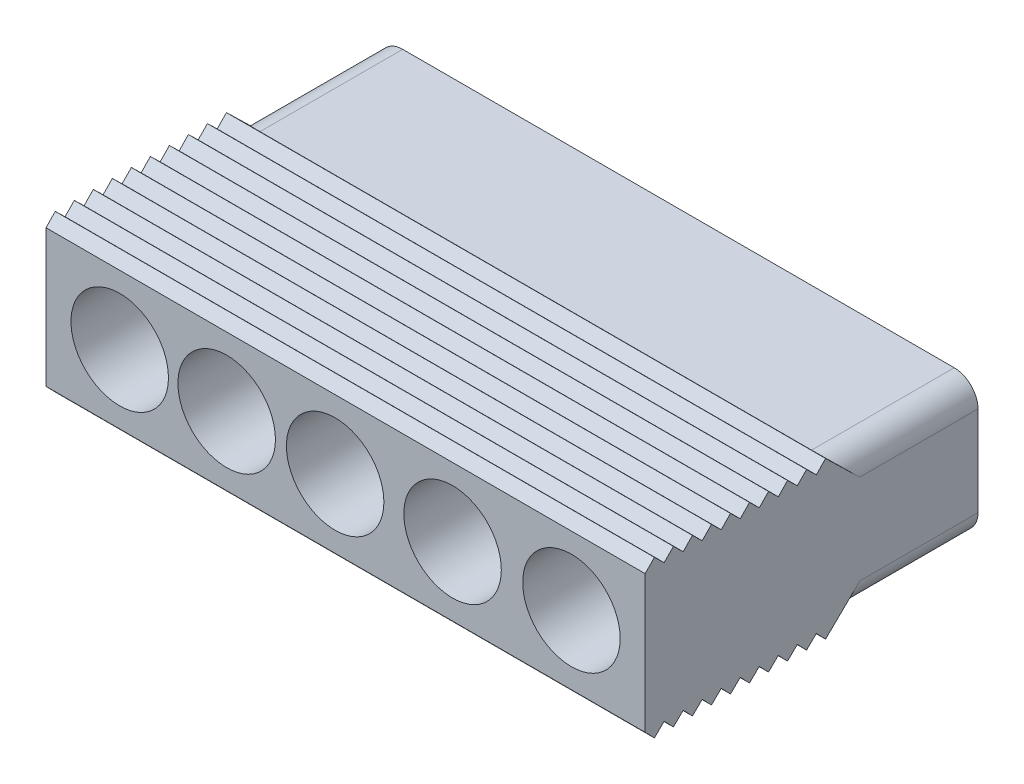
SolidWorks part; units mm, degrees
ref_plane "Front Plane" through (0, 0, 0) normal (0, 0, 1) x (1, 0, 0)
ref_plane "Top Plane" through (0, 0, 0) normal (0, 1, 0) x (1, 0, 0)
ref_plane "Right Plane" through (0, 0, 0) normal (1, 0, 0) x (0, 0, -1)
sketch "Sketch1" plane through (0, 0, 0) normal (0, 0, 1) x (1, 0, 0)
  line L0 (7.22, 0.6895) -> (-11.78, 0.6895) construction
  line L1 (-14.88, -2.2005) -> (10.32, -2.2005)
  line L2 (-14.88, -2.2005) -> (-14.88, 3.5795)
  line L3 (-14.88, 3.5795) -> (10.32, 3.5795)
  line L4 (10.32, -2.2005) -> (10.32, 3.5795)
  line L5 (-14.88, -2.2005) -> (10.32, 3.5795) construction
  line L6 (-14.88, 3.5795) -> (10.32, -2.2005) construction
  circle A2 centre (7.22, 0.6895) radius 2 construction
  circle A3 centre (-11.78, 0.6895) radius 2 construction
  circle A4 centre (7.22, -3.7005) radius 1.5 construction
  point P0 (-2.28, 0.6895)
  point P6 (0, 0.6895)
  point P13 (0, 0)
  point P14 (0, 0)
  point P16 (0, 0)
  dimension "D1" = 3.1
  dimension "D2" = 3.1
extrude "Boss-Extrude1" add sketch "Sketch1" along normal blind 14 contours L2 L3 L4 L1
sketch "Sketch2" plane through (0, 0, 14) normal (0, 0, 1) x (1, 0, 0)
  circle A0 centre (-11.78, 0.6895) radius 2.05
  circle A7 centre (-7.28, 0.6895) radius 2.05
  circle A8 centre (-2.7182, 0.6895) radius 2.05
  circle A9 centre (2.22, 0.6895) radius 2.05
  circle A10 centre (7.22, 0.6895) radius 2.05
  point P2 (-11.6648, 0.8497)
  point P3 (-11.78, 0.6895)
  point P7 (-7.02, 1.4356)
  point P8 (-7.28, 0.6895)
  point P10 (-4.1203, 2.5257)
  point P12 (-2.7182, 0.6895)
  point P15 (5.3592, 1.4356)
  point P16 (6.9344, 0.6895)
  point P17 (4.4464, 5.5194)
  point P18 (2.22, 0.6895)
  point P21 (7.22, 0.6895)
  point P22 (-2.5582, 0.9645)
  point P23 (-3.8596, 7.5864)
  dimension "D1" = 4.1
extrude "Cut-Extrude1" cut sketch "Sketch2" against normal offset from surface (13.1 mm away) 0.9
sketch "Sketch4" plane through (0, 0, 14) normal (0, 0, 1) x (1, 0, 0)
  circle A0 centre (7.22, 0.6895) radius 1.775
  circle A1 centre (2.22, 0.6895) radius 1.775
  circle A2 centre (-2.7182, 0.6895) radius 1.775
  circle A3 centre (-7.28, 0.6895) radius 1.775
  circle A4 centre (-11.78, 0.6895) radius 1.775
  point P5 (2.22, 0.6895)
  point P9 (-2.7182, 0.6895)
  point P13 (-7.28, 0.6895)
  point P17 (-11.78, 0.6895)
  dimension "D1" = 3.55
extrude "Cut-Extrude2" cut sketch "Sketch4" against normal up to next
sketch "Sketch5" plane through (0, -2.2005, 0) normal (0, -1, 0) x (1, 0, 0)
  line L0 (10.2813, 5.116) -> (4.5537, 5.116) construction
  line L3 (4.9888, 5.116) -> (-0.1538, 5.116) construction
  line L4 (0.2305, 5.116) -> (-5.3955, 5.116) construction
  line L5 (-4.3174, 5.116) -> (-9.8476, 5.116) construction
  line L6 (-8.6, 5.116) -> (-14.565, 5.116) construction
  text T0 "A" font "Arial" height in points 15
  text T1 "B" font "Arial" height in points 15
  text T2 "0" font "Arial" height in points 15
  text T3 "1" font "Arial" height in points 15
  text T4 "2\r\n" font "Arial" height in points 15
  point P3 (0, 0)
extrude "Boss-Extrude2" add sketch "Sketch5" along normal blind 0.3
sketch "Sketch6" plane through (10.32, 0, 0) normal (1, 0, 0) x (0, 0, -1)
  line L0 (-14, -2.2005) -> (-13.6106, -2.6004)
  line L3 (-13.6106, -2.6004) -> (-13.2, -2.2005)
  line L4 (-14, -2.2005) -> (0, -2.2005) construction
  line L5 (-13.2, -2.2005) -> (-14, -2.2005)
  point P2 (-13.7497, -2.4575)
  dimension "D1" = 0.8
extrude "Boss-Extrude3" add sketch "Sketch6" against normal up to surface (25.2 mm away) contours L3 L5 L0 up to face at (-14.88, 0.6895, 7)
pattern_linear "LPattern1" count 10 spacing 0.8 along (0, 0, -1) of "Boss-Extrude3"
ref_plane "Plane1" through (0, 0.6895, 0) normal (0, -1, 0) x (-1, 0, 0)
mirror "Mirror1" about plane through (0, 0.6895, 0) normal (0, -1, 0) of "LPattern1", "Boss-Extrude3"
fillet "Fillet1" radius 1 4 edges at (10.32, 3.5795, 3) (10.32, -2.2005, 3) (-14.88, 3.5795, 3) (-14.88, -2.2005, 3)
